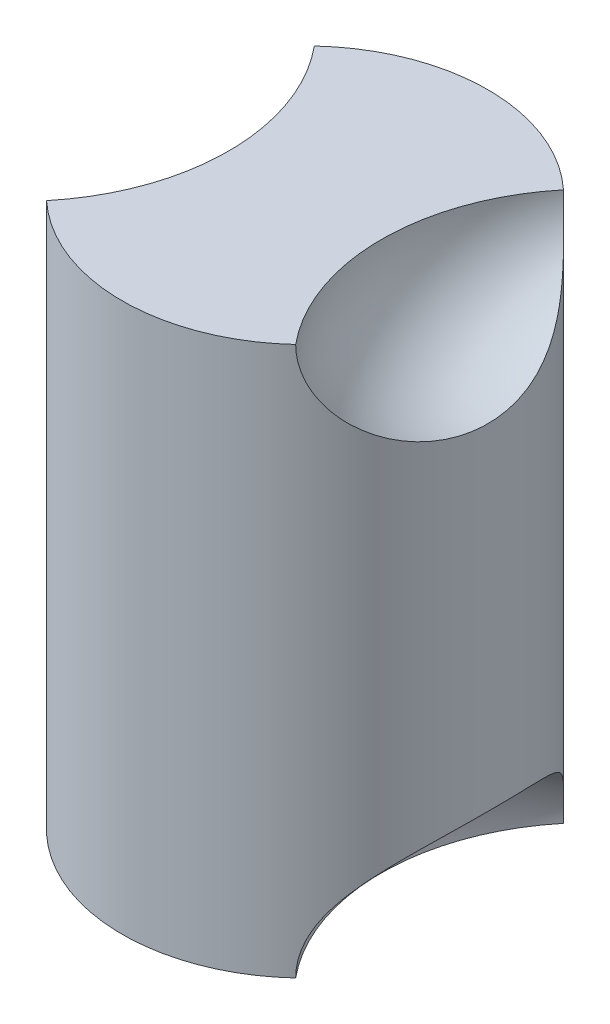
SolidWorks part; units mm, degrees
ref_plane "Front Plane" through (0, 0, 0) normal (0, 0, 1) x (1, 0, 0)
ref_plane "Top Plane" through (0, 0, 0) normal (0, 1, 0) x (1, 0, 0)
ref_plane "Right Plane" through (0, 0, 0) normal (1, 0, 0) x (0, 0, -1)
sketch "Sketch1" plane through (0, 0, 0) normal (0, 1, 0) x (1, 0, 0)
  circle A0 centre (0, 0) radius 12.7
  dimension "D1" = 25.4
extrude "Boss-Extrude1" add sketch "Sketch1" along normal blind 38.1 contours A0
ref_plane "Plane1" through (12.7, 0, 0) normal (1, 0, 0) x (0, 0, -1)
sketch "Sketch2" plane through (12.7, 0, 0) normal (1, 0, 0) x (0, 0, -1)
  line L0 (-12.7, 38.1) -> (12.7, 38.1) construction
  line L1 (-12.7, 0) -> (12.7, 0) construction
  line L2 (-12.7, 38.1) -> (12.7, 38.1)
  arc A0 (-12.7, 38.1) -> (12.7, 38.1) centre (0, 45.3122) ccw
revolve "Cut-Revolve1" cut sketch "Sketch2" angle 360 about L2
sketch "Sketch3" plane through (12.7, 0, 0) normal (1, 0, 0) x (0, 0, -1)
  line L0 (-12.7, 0) -> (12.7, 0) construction
  line L1 (-12.7, 0) -> (12.7, 0)
  arc A0 (-12.7, 0) -> (12.7, 0) centre (0, -7.2122) cw
revolve "Cut-Revolve2" cut sketch "Sketch3" angle 360 about L0
ref_plane "Plane2" through (-12.7, 0, 0) normal (1, 0, 0) x (0, 0, -1)
sketch "Sketch4" plane through (-12.7, 0, 0) normal (1, 0, 0) x (0, 0, -1)
  line L0 (-12.7, 38.1) -> (12.7, 38.1) construction
  line L1 (-12.7, 38.1) -> (12.7, 38.1)
  arc A0 (-12.7, 38.1) -> (12.7, 38.1) centre (0, 45.3122) ccw
revolve "Cut-Revolve3" cut sketch "Sketch4" angle 360 about L0
sketch "Sketch5" plane through (-12.7, 0, 0) normal (1, 0, 0) x (0, 0, -1)
  line L0 (0, 0) -> (-12.7, 0) construction
  line L1 (0, 0) -> (12.6649, 0) construction
  line L2 (-12.7, 0) -> (12.6649, 0)
  arc A0 (-12.7, 0) -> (12.6649, 0) centre (-0.0175, -7.243) cw
revolve "Cut-Revolve4" cut sketch "Sketch5" angle 360 about L0
